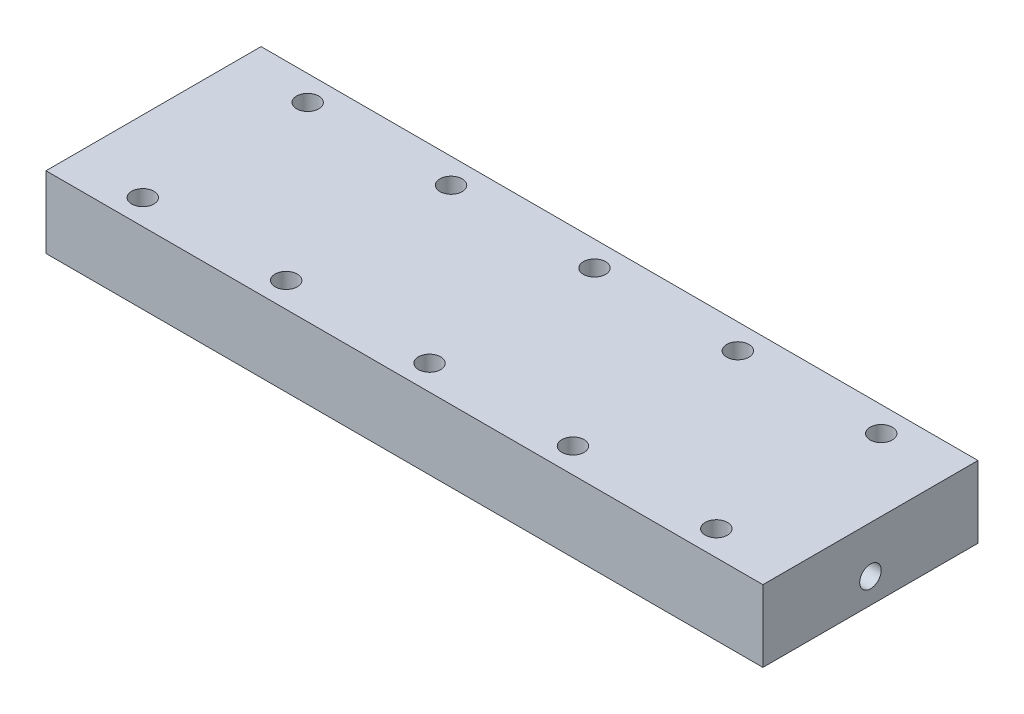
SolidWorks part; units mm, degrees
ref_plane "Front Plane" through (0, 0, 0) normal (0, 0, 1) x (1, 0, 0)
ref_plane "Top Plane" through (0, 0, 0) normal (0, 1, 0) x (1, 0, 0)
ref_plane "Right Plane" through (0, 0, 0) normal (1, 0, 0) x (0, 0, -1)
sketch "Sketch1" plane through (0, 0, 0) normal (0, 1, 0) x (1, 0, 0)
  line L0 (-50, 0) -> (50, 0)
  line L1 (50, 0) -> (50, 30)
  line L2 (50, 30) -> (-50, 30)
  line L3 (-50, 30) -> (-50, 0)
  dimension "D1" = 100
  dimension "D2" = 50
  dimension "D3" = 30
  dimension "D4" = 30
extrude "Boss-Extrude1" add sketch "Sketch1" along normal blind 10
sketch "Sketch2" plane through (0, 0, 0) normal (0, 1, 0) x (1, 0, 0)
  line L0 (45, 24) -> (45, 6)
  line L1 (45, 6) -> (15, 6)
  line L2 (15, 6) -> (15, 24)
  line L3 (15, 24) -> (45, 24)
  line L4 (-50, 0) -> (50, 0) construction
  line L6 (50, 0) -> (50, 30) construction
  dimension "D1" = 18
  dimension "D2" = 6
  dimension "D3" = 30
  dimension "D4" = 5
extrude "Cut-Extrude1" cut sketch "Sketch2" against normal blind 8.5 and the other way blind 8.5
sketch "Sketch4" plane through (0, 0, 0) normal (0, 1, 0) x (1, 0, 0)
  line L0 (15, 6) -> (25, 6)
  line L1 (45, 6) -> (15, 6) construction
  line L2 (25, 6) -> (25, 24)
  line L3 (15, 24) -> (45, 24) construction
  line L4 (25, 24) -> (15, 24)
  line L5 (15, 24) -> (15, 6)
  dimension "D1" = 10
extrude "Boss-Extrude2" add sketch "Sketch4" along normal blind 10
sketch "Sketch3" plane through (0, 0, 0) normal (0, 1, 0) x (1, 0, 0)
  line L0 (50, 15) -> (-50, 15) construction
  line L1 (50, 0) -> (50, 30) construction
  line L2 (-50, 30) -> (-50, 0) construction
  line L3 (-45, 15) -> (-45, 8.41)
  line L4 (-45, 8.41) -> (35, 6.89)
  line L5 (35, 6.89) -> (35, 15)
  line L6 (35, 15) -> (-45, 15)
  line L8 (25, 6) -> (25, 24) construction
  dimension "D1" = 80
  dimension "D3" = 8.11
  dimension "D4" = 6.59
  dimension "D5" = 10
revolve "Cut-Revolve1" cut sketch "Sketch3" angle 360 about L0
sketch "Sketch6" plane through (0, 0, 0) normal (0, 1, 0) x (1, 0, 0)
  line L0 (-50, 15) -> (47.3429, 15) construction
  line L1 (-50, 30) -> (-50, 0) construction
  line L2 (25, 22.92) -> (25, 20.42)
  line L3 (25, 20.42) -> (15.0477, 20.23)
  line L4 (15.0477, 20.23) -> (15, 22.73)
  line L5 (-45, 21.59) -> (25, 22.92) construction
  line L6 (15, 22.73) -> (25, 22.92)
  dimension "D1" = 10
  dimension "D2" = 2.5
  dimension "D3" = 2.5
revolve "Revolve1" add sketch "Sketch6" angle 180 about L0
sketch "Sketch7" plane through (0, 0, 0) normal (0, 1, 0) x (1, 0, 0)
  line L0 (-45, 15) -> (38.1554, 15) construction
  line L1 (-45, 8.41) -> (-45, 21.59) construction
  line L2 (-35, 21.78) -> (-22.5, 22.0175)
  line L3 (-45, 21.59) -> (15, 22.73) construction
  line L4 (-22.5, 22.0175) -> (-22.5, 19.5175)
  line L5 (-22.5, 19.5175) -> (-35, 19.28)
  line L6 (-35, 19.28) -> (-35, 21.78)
  dimension "D1" = 2.5
  dimension "D2" = 2.5
  dimension "D3" = 12.5
  dimension "D4" = 10
revolve "Revolve2" add sketch "Sketch7" angle 180 about L0
sketch "Sketch8" plane through (0, 0, 0) normal (0, 1, 0) x (1, 0, 0)
  line L0 (-45, 15) -> (32.5702, 15) construction
  line L1 (-45, 8.41) -> (-45, 21.59) construction
  line L2 (-10, 22.255) -> (-10, 19.755)
  line L3 (-22.5, 22.0175) -> (15, 22.73) construction
  line L4 (-10, 19.755) -> (2.5, 19.9925)
  line L5 (2.5, 19.9925) -> (2.5, 22.4925)
  line L6 (2.5, 22.4925) -> (-10, 22.255)
  dimension "D1" = 12.5
  dimension "D2" = 2.5
  dimension "D3" = 2.5
  dimension "D4" = 12.5
revolve "Revolve3" add sketch "Sketch8" angle 180 about L0
ref_plane "Plane1" through (-50, 0, 0) normal (-1, 0, 0) x (0, 0, 1)
sketch "Sketch9" plane through (-50, 0, 0) normal (-1, 0, 0) x (0, 0, 1)
  line L0 (0, 10) -> (0, 0) construction
  line L1 (-30, 0) -> (0, 0) construction
  circle A0 centre (-15, 3.5) radius 1
  dimension "D2" = 2
  dimension "D1" = 15
  dimension "D3" = 3.5
extrude "Cut-Extrude2" cut sketch "Sketch9" against normal blind 12
ref_plane "Plane2" through (50, 0, 0) normal (1, 0, 0) x (0, 0, -1)
sketch "Sketch10" plane through (50, 0, 0) normal (1, 0, 0) x (0, 0, -1)
  circle A0 centre (15, 3.5) radius 1.5
  dimension "D1" = 3
extrude "Cut-Extrude3" cut sketch "Sketch10" against normal blind 12
fillet "Fillet3" radius 1.2 10 edges at (15.0477, 5.23, -15) (15, 7.73, -15) (-10, 7.255, -15) (2.5, 7.4925, -15) (2.5, 4.9925, -15) (-10, 4.755, -15) (-22.5, 7.0175, -15) (-22.5, 4.5175, -15) (-35, 6.78, -15) (-35, 4.28, -15)
fillet "Fillet5" radius 1.25 1 edges at (25, 5.42, -15)
fillet "Fillet7" radius 2 8 edges at (25, 4.25, -24) (25, 4.25, -6) (45, 4.25, -24) (35, 8.5, -24) (45, 4.25, -6) (45, 8.5, -15) (35, 8.5, -6) (25, 8.5, -15)
sketch "Sketch11" plane through (0, 0, 0) normal (0, 1, 0) x (1, 0, 0)
  line L0 (-50, 5.5) -> (-50, -5.5) construction
  line L2 (-50, 0) -> (50, 0) construction
  line L3 (-50, 0) -> (50, 0) construction
  line L4 (50, 30) -> (-50, 30) construction
  line L5 (-50, 30) -> (-50, 0) construction
  circle A0 centre (-40, 3.5) radius 1.55
  circle A1 centre (-20, 3.5) radius 1.55
  circle A2 centre (0, 3.5) radius 1.55
  circle A3 centre (20, 3.5) radius 1.55
  circle A4 centre (40, 3.5) radius 1.55
  circle A5 centre (-40, 26.5) radius 1.55
  circle A6 centre (-20, 26.5) radius 1.55
  circle A7 centre (0, 26.5) radius 1.55
  circle A8 centre (20, 26.5) radius 1.55
  circle A9 centre (40, 26.5) radius 1.55
  dimension "D11" = 3.1
  dimension "D12" = 3.1
  dimension "D13" = 3.1
  dimension "D14" = 3.1
  dimension "D15" = 3.1
  dimension "D17" = 3.1
  dimension "D18" = 3.1
  dimension "D21" = 3.1
  dimension "D23" = 3.1
  dimension "D25" = 3.1
  dimension "D1" = 10
  dimension "D2" = 20
  dimension "D3" = 20
  dimension "D4" = 20
  dimension "D5" = 20
  dimension "D6" = 3.5
  dimension "D7" = 3.5
  dimension "D8" = 3.5
  dimension "D9" = 3.5
  dimension "D10" = 3.5
  dimension "D16" = 3.5
  dimension "D19" = 3.5
  dimension "D20" = 3.5
  dimension "D22" = 3.5
  dimension "D24" = 3.5
  dimension "D26" = 10
  dimension "D27" = 20
  dimension "D28" = 20
  dimension "D29" = 20
  dimension "D30" = 20
extrude "Cut-Extrude4" cut sketch "Sketch11" against normal blind 20 and the other way blind 20
